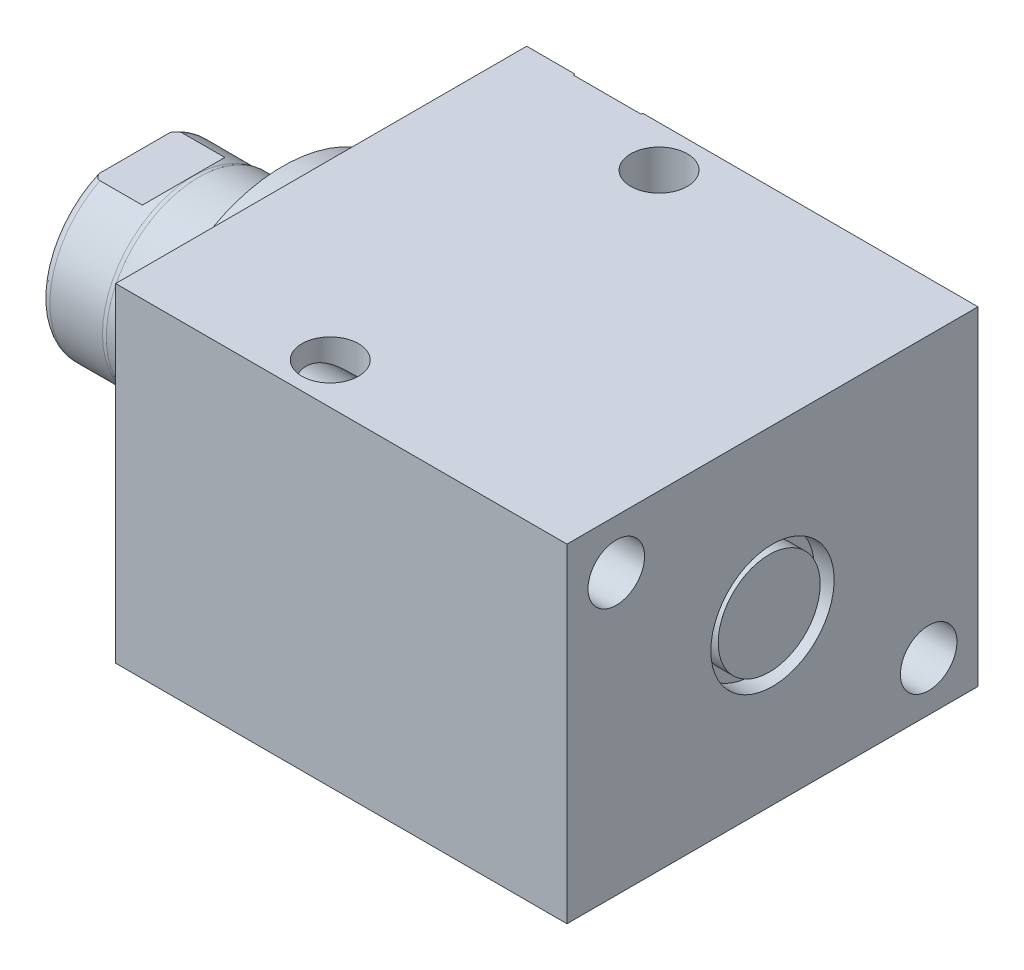
SolidWorks part; units mm, degrees
material "Alloy Steel"
ref_plane "Front Plane" through (0, 0, 0) normal (0, 0, 1) x (1, 0, 0)
ref_plane "Top Plane" through (0, 0, 0) normal (0, 1, 0) x (1, 0, 0)
ref_plane "Right Plane" through (0, 0, 0) normal (1, 0, 0) x (0, 0, -1)
ref_plane "Plane1" through (0, 0, 0) normal (1, 0, 0) x (0, 0, -1)
sketch "Sketch1" plane through (0, 0, 0) normal (1, 0, 0) x (0, 0, -1)
  line L0 (-31.75, 25.4) -> (31.75, 25.4)
  line L1 (31.75, 25.4) -> (31.75, -25.4)
  line L2 (31.75, -25.4) -> (-31.75, -25.4)
  line L3 (-31.75, -25.4) -> (-31.75, 25.4)
  line L4 (0, -24.4475) -> (0, 24.4475) construction
  dimension "D1" = 50.8
  dimension "D2" = 25.4
  dimension "D3" = 63.5
extrude "Extrude1" add sketch "Sketch1" along normal blind 69.723
ref_plane "Plane12" through (0, 17.4498, 0) normal (0, 1, 0) x (-1, 0, 0)
sketch "S2D0002" plane through (0, 17.4498, 0) normal (0, 1, 0) x (-1, 0, 0)
  line L0 (-18.8849, -31.496) -> (-22.225, -31.496)
  line L1 (-18.8849, -31.496) -> (-18.3423, -28.9433)
  line L2 (-18.3423, -28.9433) -> (-17.6784, -28.2794)
  line L3 (-17.6784, -28.2794) -> (-17.6784, -17.526)
  line L4 (-17.6784, -17.526) -> (-12.7, -17.526)
  line L5 (-12.7, -17.526) -> (-12.7, -31.75)
  line L6 (-12.7, -19.1384) -> (-12.7, 0.6985) construction
  line L7 (0, -31.75) -> (0, 31.75) construction
  line L8 (-22.225, -31.75) -> (-22.225, -31.496)
  line L9 (-69.723, -31.75) -> (0, -31.75) construction
  line L10 (-22.225, -31.75) -> (-12.7, -31.75)
  dimension "D1" = 14.224
  dimension "D2" = 12.7
  dimension "D3" = 9.9568
  dimension "D4" = 45
  dimension "D5" = 12.3698
  dimension "D6" = 12
  dimension "D7" = 2.5527
  dimension "D8" = 0.254
  dimension "D9" = 19.05
revolve "Cut-Revolve1" cut sketch "S2D0002" angle 360 about L6
ref_plane "Plane3" through (41.148, 0, -25.146) normal (0, 1, 0) x (1, 0, 0)
sketch "Sketch3" plane through (41.148, 0, -25.146) normal (0, 1, 0) x (1, 0, 0)
  line L0 (18.8849, 6.35) -> (22.225, 6.35)
  line L1 (18.8849, 6.35) -> (18.3423, 3.7973)
  line L2 (18.3423, 3.7973) -> (17.6784, 3.1334)
  line L3 (17.6784, 3.1334) -> (17.6784, -7.62)
  line L4 (17.6784, -7.62) -> (12.7, -7.62)
  line L5 (12.7, -7.62) -> (12.7, 6.604)
  line L6 (12.7, -21.9564) -> (12.7, 0.6985) construction
  line L7 (-41.148, 6.604) -> (-41.148, -56.896) construction
  line L8 (22.225, 6.604) -> (22.225, 6.35)
  line L9 (28.575, 6.604) -> (-23.2021, 6.604) construction
  line L10 (22.225, 6.604) -> (12.7, 6.604)
  dimension "D1" = 14.224
  dimension "D2" = 53.848
  dimension "D3" = 9.9568
  dimension "D4" = 45
  dimension "D5" = 12
  dimension "D6" = 12.3698
  dimension "D7" = 2.5527
  dimension "D8" = 0.254
  dimension "D9" = 19.05
revolve "Cut-Revolve2" cut sketch "Sketch3" angle 360 about L6
ref_plane "Plane4" through (53.975, 0, 0) normal (0, 0, 1) x (0, -1, 0)
sketch "Sketch4" plane through (53.975, 0, 0) normal (0, 0, 1) x (0, -1, 0)
  line L0 (6.1849, 12.7) -> (9.525, 12.7)
  line L1 (6.1849, 12.7) -> (5.6423, 10.1473)
  line L2 (5.6423, 10.1473) -> (4.9784, 9.4834)
  line L3 (4.9784, 9.4834) -> (4.9784, 1.3462)
  line L4 (4.9784, 1.3462) -> (0, 1.3462)
  line L5 (0, 1.3462) -> (0, 15.748)
  line L6 (0, -15.0954) -> (0, 0.5677) construction
  line L7 (0, 15.748) -> (9.525, 15.748)
  line L9 (-25.4, 15.748) -> (25.4, 15.748) construction
  line L10 (9.525, 15.748) -> (9.525, 12.7)
  dimension "D1" = 11.3538
  dimension "D2" = 9.9568
  dimension "D3" = 3.048
  dimension "D4" = 19.05
  dimension "D5" = 2.5527
  dimension "D6" = 12
  dimension "D7" = 45
  dimension "D8" = 12.3698
revolve "Cut-Revolve3" cut sketch "Sketch4" angle 360 about L6
sketch "Sketch5" plane through (0, 0, 0) normal (-1, 0, 0) x (0, 0, 1)
  circle A0 centre (0, 0) radius 22.225
  dimension "D1" = 44.45
extrude "Extrude2" add sketch "Sketch5" along normal blind 5.969
ref_plane "Plane5" through (0, 0, 0) normal (0, -1, 0) x (0, 0, 1)
sketch "Sketch6" plane through (0, 0, 0) normal (0, -1, 0) x (0, 0, 1)
  line L0 (0, 5.969) -> (-14.2875, 5.969)
  line L1 (-14.2875, 5.969) -> (-14.2875, 28.829)
  line L2 (-14.2875, 28.829) -> (0, 28.829)
  line L3 (0, 28.829) -> (0, 5.969)
  line L4 (0, -5.7546) -> (0, 21.1709) construction
  line L5 (22.225, 5.969) -> (-22.225, 5.969) construction
  line L6 (31.75, -69.723) -> (-31.75, -69.723) construction
  dimension "D1" = 98.552
  dimension "D2" = 28.575
revolve "Revolve1" add sketch "Sketch6" angle 360 about L4
ref_plane "Plane6" through (-18.5113, 3.2639, 0) normal (0, 0, 1) x (0, 1, 0)
sketch "S2D0001" plane through (-18.5113, 3.2639, 0) normal (0, 0, 1) x (0, 1, 0)
  line L0 (2.286, 8.25) -> (2.286, -6.5225)
  line L1 (2.286, -6.5225) -> (-3.2639, -6.5225)
  line L2 (3.4798, 10.3177) -> (-3.2639, 10.3177)
  line L3 (-3.2639, 10.3177) -> (-3.2639, -6.5225)
  line L4 (2.286, 8.25) -> (3.4798, 10.3177)
  line L5 (-3.2639, -18.5113) -> (-3.2639, 2.765) construction
  line L6 (11.0236, 10.3177) -> (-17.5514, 10.3177) construction
  dimension "D1" = 30
  dimension "D2" = 13.4874
  dimension "D3" = 11.0998
  dimension "D4" = 16.8402
revolve "Cut-Revolve4" cut sketch "S2D0001" angle 360 about L5
ref_plane "Plane7" through (0, 0, 0) normal (0, 1, 0) x (0, 0, -1)
sketch "Sketch8" plane through (0, 0, 0) normal (0, 1, 0) x (0, 0, -1)
  line L0 (-14.2875, 18.923) -> (-14.097, 19.685)
  line L1 (-14.097, 19.685) -> (-14.097, 27.813)
  line L2 (0, 12.6594) -> (0, 20.8178) construction
  line L3 (-14.2875, 18.923) -> (-14.2875, 28.829)
  line L4 (-13.7089, 28.829) -> (-14.2875, 28.829)
  line L5 (14.2875, 28.829) -> (-14.2875, 28.829) construction
  line L6 (-14.2875, 28.829) -> (-14.2875, 5.969) construction
  arc A0 (-13.7089, 28.829) -> (-14.097, 27.813) centre (-12.573, 27.813) ccw
  dimension "D2" = 1.524
  dimension "D1" = 28.194
  dimension "D3" = 1.016
  dimension "D4" = 0.762
  dimension "D5" = 9.144
revolve "Cut-Revolve5" cut sketch "Sketch8" angle 360 about L2
ref_plane "Plane11" through (0, 0, 0) normal (0, 0, -1) x (0, -1, 0)
sketch "Sketch12" plane through (0, 0, 0) normal (0, 0, -1) x (0, -1, 0)
  line L0 (12.573, 28.829) -> (12.573, 21.2598)
  line L1 (12.573, 21.2598) -> (14.097, 19.7358)
  line L2 (-12.573, 28.829) -> (-12.573, 21.2598)
  line L3 (-12.573, 21.2598) -> (-14.097, 19.7358)
  line L4 (12.573, 28.829) -> (14.097, 28.829)
  line L5 (0, 13.7262) -> (0, 20.767) construction
  line L6 (-14.097, 19.7358) -> (-14.097, 28.829)
  line L7 (13.7089, 28.829) -> (-13.7089, 28.829) construction
  line L8 (14.097, 19.685) -> (14.097, 27.813) construction
  line L9 (14.097, 19.7358) -> (14.097, 28.829)
  line L10 (-12.573, 28.829) -> (-14.097, 28.829)
  dimension "D1" = 25.146
  dimension "D2" = 7.5692
  dimension "D3" = 45
extrude "Cut-Extrude4" cut sketch "Sketch12" against normal mid plane 60.96
sketch "Sketch13" plane through (0, 0, -31.496) normal (0, 0, -1) x (-1, 0, 0)
  circle A0 centre (-53.848, 0) radius 7.874
  circle A2 centre (-53.848, 0) radius 6.1849 construction
  dimension "D1" = 15.748
extrude "Extrude3" add sketch "Sketch13" along normal blind 2.54
hole_wizard "Hole1" positions "Sketch15" profile "Sketch14" legacy end condition up to next
sketch "Sketch15" plane through (0, 0, 0) normal (-1, 0, 0) x (0, 0, 1)
  line L0 (0, 0) -> (-29.9914, 0) construction
  line L1 (0, 0) -> (0, 25.7648) construction
  point P0 (-24.13, -17.78)
  point P11 (24.13, 17.78)
  dimension "D1" = 17.78
  dimension "D2" = 24.13
  dimension "D3" = 35.56
  dimension "D4" = 48.26
sketch "Sketch14" plane through (0, -17.78, -24.13) normal (0, 1, 0) x (0, 0, 1)
  line L0 (0, 0) -> (0, 69.723)
  line L1 (0, 69.723) -> (4.3688, 69.723)
  line L2 (4.3688, 69.723) -> (4.3688, 0)
  line L3 (4.3688, 0) -> (0, 0)
  line L4 (0, 110) -> (0, -10) construction
  dimension "Diameter" = 8.7376
  dimension "Depth" = 69.723
hole_wizard "Hole2" positions "Sketch17" profile "Sketch16" legacy
sketch "Sketch17" plane through (0, 25.4, 0) normal (0, 1, 0) x (-1, 0, 0)
  line L0 (0, 0) -> (-59.3363, 0) construction
  line L1 (0, -31.75) -> (0, 31.75) construction
  point P0 (-26.797, -25.4)
  point P9 (-26.797, 25.4)
  dimension "D1" = 50.8
  dimension "D2" = 26.797
sketch "Sketch16" plane through (26.797, 25.4, -25.4) normal (1, 0, 0) x (0, 0, 1)
  line L0 (0, 0) -> (0, 50.8)
  line L1 (0, 50.8) -> (4.3688, 50.8)
  line L2 (4.3688, 50.8) -> (4.3688, 0)
  line L3 (4.3688, 0) -> (0, 0)
  line L4 (0, 110) -> (0, -10) construction
  dimension "Diameter" = 8.7376
  dimension "Depth" = 50.8
sketch "Sketch18" plane through (66.675, 0, 0) normal (1, 0, 0) x (0, 0, -1)
  circle A0 centre (0, 0) radius 7.874
  dimension "D1" = 15.748
extrude "Extrude4" add sketch "Sketch18" along normal blind 2.54
